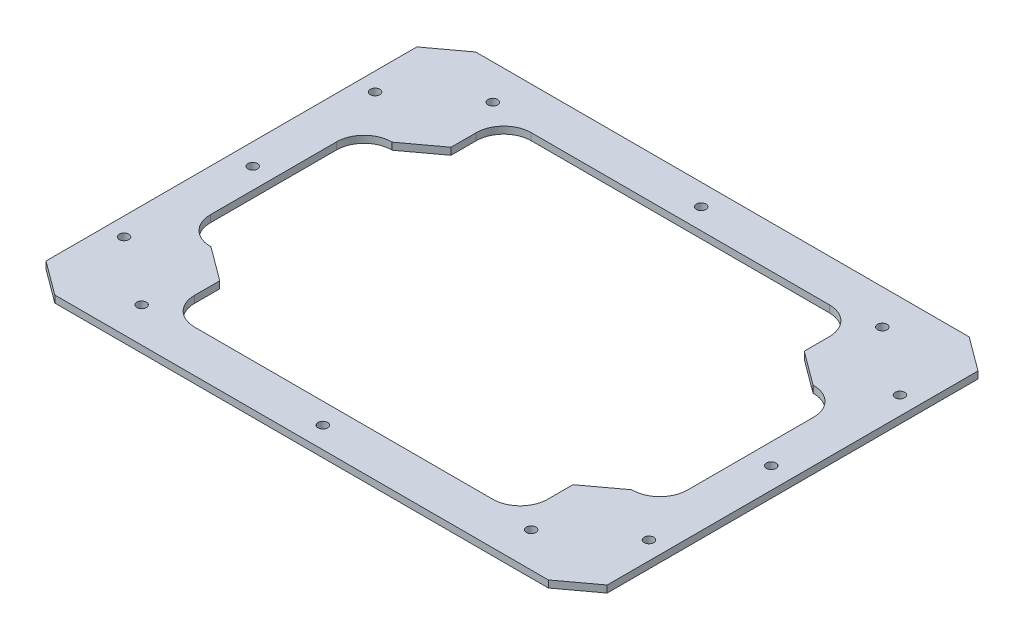
SolidWorks part; units mm, degrees
material "Thornel Mat VMA"
ref_plane "Front Plane" through (0, 0, 0) normal (0, 0, 1) x (1, 0, 0)
ref_plane "Top Plane" through (0, 0, 0) normal (0, 1, 0) x (1, 0, 0)
ref_plane "Right Plane" through (0, 0, 0) normal (1, 0, 0) x (0, 0, -1)
sketch "Sketch1" plane through (0, 0, 0) normal (0, 1, 0) x (1, 0, 0)
  line L0 (-127, 83.9186) -> (-111.6865, 95.25)
  line L1 (-127, -95.25) -> (127, -95.25)
  line L2 (-127, -95.25) -> (-127, 95.25)
  line L3 (-127, 95.25) -> (127, 95.25)
  line L4 (127, -95.25) -> (127, 95.25)
  line L5 (-107.95, 28.565) -> (-107.95, -28.565)
  line L8 (-95.504, 41.011) -> (-95.25, 41.011)
  line L10 (-127, 95.25) -> (127, -95.25) construction
  line L12 (127, 83.9186) -> (111.6865, 95.25)
  line L14 (79.9365, 52.3423) -> (79.9365, 63.754)
  line L15 (95.25, 41.011) -> (79.9365, 52.3423)
  line L16 (95.504, 41.011) -> (95.25, 41.011)
  line L17 (107.95, 28.565) -> (107.95, -28.565)
  line L18 (127, -83.9186) -> (111.6865, -95.25)
  line L19 (95.504, -41.011) -> (95.25, -41.011)
  line L20 (95.25, -41.011) -> (79.9365, -52.3423)
  line L21 (79.9365, -52.3423) -> (79.9365, -63.754)
  line L22 (127, 0) -> (-127, 0) construction
  line L23 (0, -13.6985) -> (0, 95.25) construction
  line L26 (-79.9365, -52.3423) -> (-79.9365, -63.754)
  line L27 (-95.25, 41.011) -> (-127, 83.9186) construction
  line L28 (-95.25, 41.011) -> (-79.9365, 52.3423)
  line L29 (-79.9365, 52.3423) -> (-79.9365, 63.754)
  line L31 (-95.25, -41.011) -> (-79.9365, -52.3423)
  line L32 (-95.504, -41.011) -> (-95.25, -41.011)
  line L33 (-127, -83.9186) -> (-111.6865, -95.25)
  line L34 (-79.9365, 52.3423) -> (-111.6865, 95.25) construction
  line L36 (-67.4905, 76.2) -> (79.9365, 76.2)
  line L37 (38.8318, 76.2) -> (67.4905, 76.2)
  line L38 (-67.4905, -76.2) -> (79.9365, -76.2)
  line L39 (38.1, -76.2) -> (67.4905, -76.2)
  arc A0 (-79.9365, 63.754) -> (-67.4905, 76.2) centre (-67.4905, 63.754) cw
  arc A1 (-107.95, 28.565) -> (-95.504, 41.011) centre (-95.504, 28.565) cw
  arc A2 (-95.504, -41.011) -> (-107.95, -28.565) centre (-95.504, -28.565) cw
  arc A3 (-67.4905, -76.2) -> (-79.9365, -63.754) centre (-67.4905, -63.754) cw
  arc A4 (79.9365, -63.754) -> (67.4905, -76.2) centre (67.4905, -63.754) cw
  arc A5 (79.9365, 63.754) -> (67.4905, 76.2) centre (67.4905, 63.754) ccw
  arc A6 (95.504, 41.011) -> (107.95, 28.565) centre (95.504, 28.565) cw
  arc A7 (95.504, -41.011) -> (107.95, -28.565) centre (95.504, -28.565) ccw
  point P0 (0, 0)
  point P1 (0, 0)
  point P14 (0, 0)
  point P22 (0, 76.2)
  point P33 (107.95, 0)
  point P35 (-79.9365, 76.2)
  point P41 (0, 0)
  point P44 (-107.95, 0)
  point P45 (-38.1, 0)
  point P46 (-31.75, 0)
  point P51 (-107.95, 41.011)
  point P54 (-107.95, -41.011)
  point P57 (-79.9365, -76.2)
  point P60 (79.9365, -76.2)
  point P63 (79.9365, 76.2)
  point P66 (107.95, 41.011)
  point P69 (107.95, -41.011)
  dimension "D8" = 12.446
  dimension "D1" = 190.5
  dimension "D2" = 254
  dimension "D3" = 19.05
  dimension "D4" = 19.05
  dimension "D5" = 143.5
  dimension "D6" = 19.05
  dimension "D7" = 12.7
extrude "Boss-Extrude1" add sketch "Sketch1" along normal blind 3.175
sketch "Sketch2" plane through (0, 3.175, 0) normal (0, 1, 0) x (1, 0, 0)
  line L0 (-87.5933, 46.6767) -> (-119.3433, 89.5843) construction
  line L1 (-95.25, 41.011) -> (-79.9365, 52.3423) construction
  line L2 (-127, 83.9186) -> (-111.6865, 95.25) construction
  line L3 (0, 0) -> (0, 95.25) construction
  line L4 (-111.6865, 95.25) -> (111.6865, 95.25) construction
  line L5 (0, 0) -> (-127, 0) construction
  line L6 (-127, -83.9186) -> (-127, 83.9186) construction
  line L7 (-103.4683, 68.1305) -> (-88.1548, 79.4619) construction
  line L8 (127, -83.9186) -> (127, 83.9186) construction
  line L9 (-111.6865, -95.25) -> (111.6865, -95.25) construction
  circle A0 centre (-88.1548, 79.4619) radius 2.159
  circle A1 centre (88.1548, 79.4619) radius 2.159
  circle A2 centre (88.1548, -79.4619) radius 2.159
  circle A3 centre (-88.1548, -79.4619) radius 2.159
  circle A4 centre (-118.7817, 56.7991) radius 2.159
  circle A5 centre (118.7817, 56.7991) radius 2.159
  circle A6 centre (-118.7817, -56.7991) radius 2.159
  circle A7 centre (118.7817, -56.7991) radius 2.159
  circle A8 centre (0, -85.598) radius 2.159
  circle A9 centre (0, 85.598) radius 2.159
  circle A10 centre (-117.348, -0.0205) radius 2.159
  circle A11 centre (117.348, -0.0205) radius 2.159
  dimension "D2" = 4.318
  dimension "D3" = 9.652
  dimension "D1" = 19.05
  dimension "D4" = 9.652
  dimension "D5" = 127
  dimension "D6" = 127
  dimension "D7" = 127
extrude "Cut-Extrude1" cut sketch "Sketch2" against normal through all
